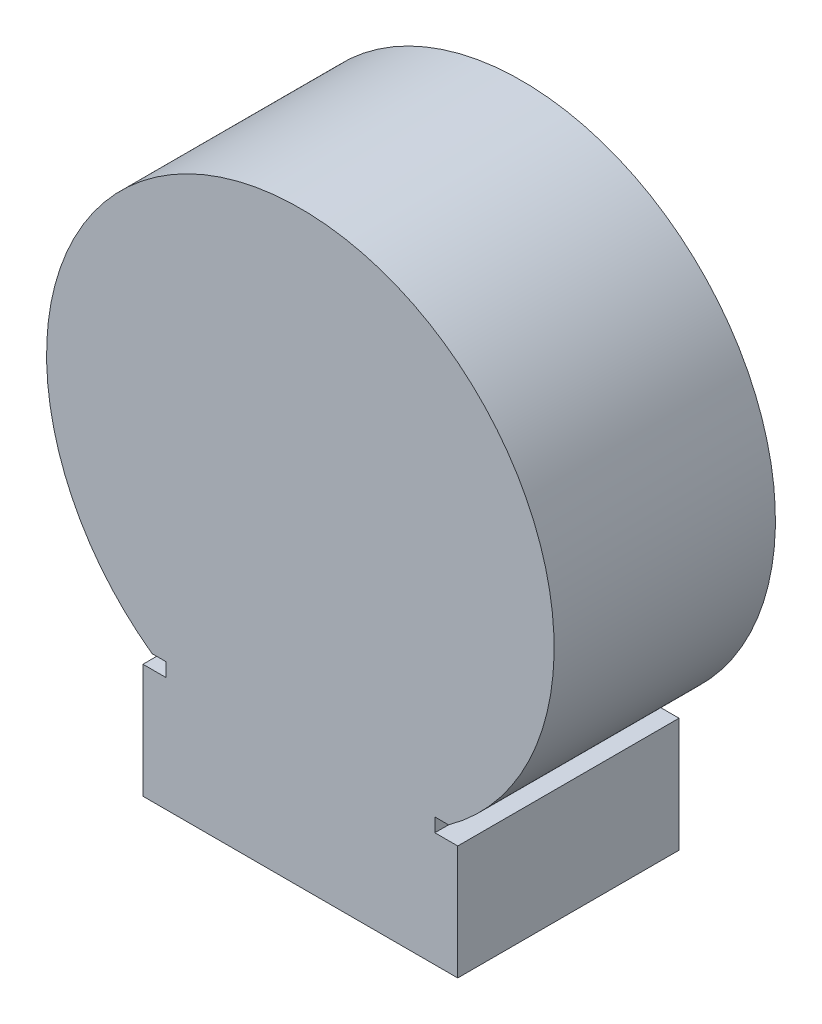
SolidWorks part; units mm, degrees
ref_plane "Front Plane" through (0, 0, 0) normal (0, 0, 1) x (1, 0, 0)
ref_plane "Top Plane" through (0, 0, 0) normal (0, 1, 0) x (1, 0, 0)
ref_plane "Right Plane" through (0, 0, 0) normal (1, 0, 0) x (0, 0, -1)
sketch "Sketch2" plane through (0, 0, 0) normal (0, 0, 1) x (1, 0, 0)
  line L0 (-8.74, 3.175) -> (-7.47, 3.175)
  line L2 (-8.74, 3.175) -> (-8.74, -3.175)
  line L3 (-8.74, -3.175) -> (8.74, -3.175)
  line L4 (8.74, 3.175) -> (8.74, -3.175)
  line L5 (-8.74, 3.175) -> (8.74, -3.175) construction
  line L6 (-8.74, -3.175) -> (8.74, 3.175) construction
  line L7 (-7.47, 3.175) -> (-7.47, 3.937)
  line L8 (-7.47, 3.937) -> (-8.232, 3.937)
  line L9 (8.74, 3.175) -> (7.47, 3.175)
  line L10 (7.47, 3.175) -> (7.47, 3.937)
  line L11 (7.47, 3.937) -> (8.232, 3.937)
  arc A0 (-8.232, 3.937) -> (8.232, 3.937) centre (0, 15.3766) cw
  point P0 (0, 0)
extrude "Boss-Extrude1" add sketch "Sketch2" along normal blind 12.29
sketch "Sketch4" plane through (0, 0, 0) normal (0, 0, -1) x (-1, 0, 0)
  circle A0 centre (0, 15.3766) radius 4.7751
